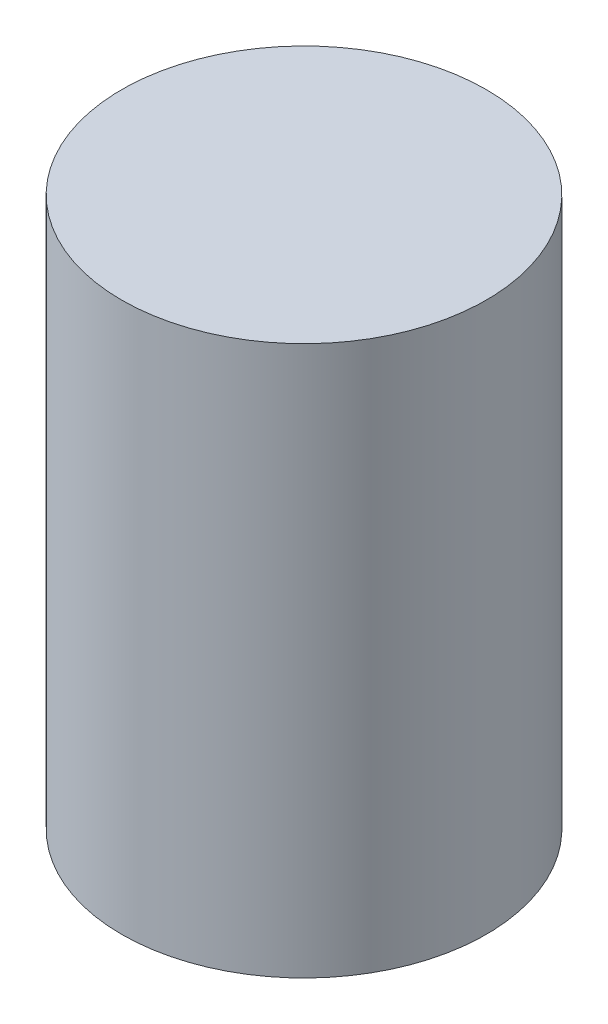
SolidWorks part; units mm, degrees
ref_plane "Front Plane" through (0, 0, 0) normal (0, 0, 1) x (1, 0, 0)
ref_plane "Top Plane" through (0, 0, 0) normal (0, 1, 0) x (1, 0, 0)
ref_plane "Right Plane" through (0, 0, 0) normal (1, 0, 0) x (0, 0, -1)
sketch "Sketch1" plane through (0, 0, 0) normal (0, 1, 0) x (1, 0, 0)
  circle A0 centre (0, 0) radius 3.05
extrude "Boss-Extrude1" add sketch "Sketch1" along normal blind 9.19
